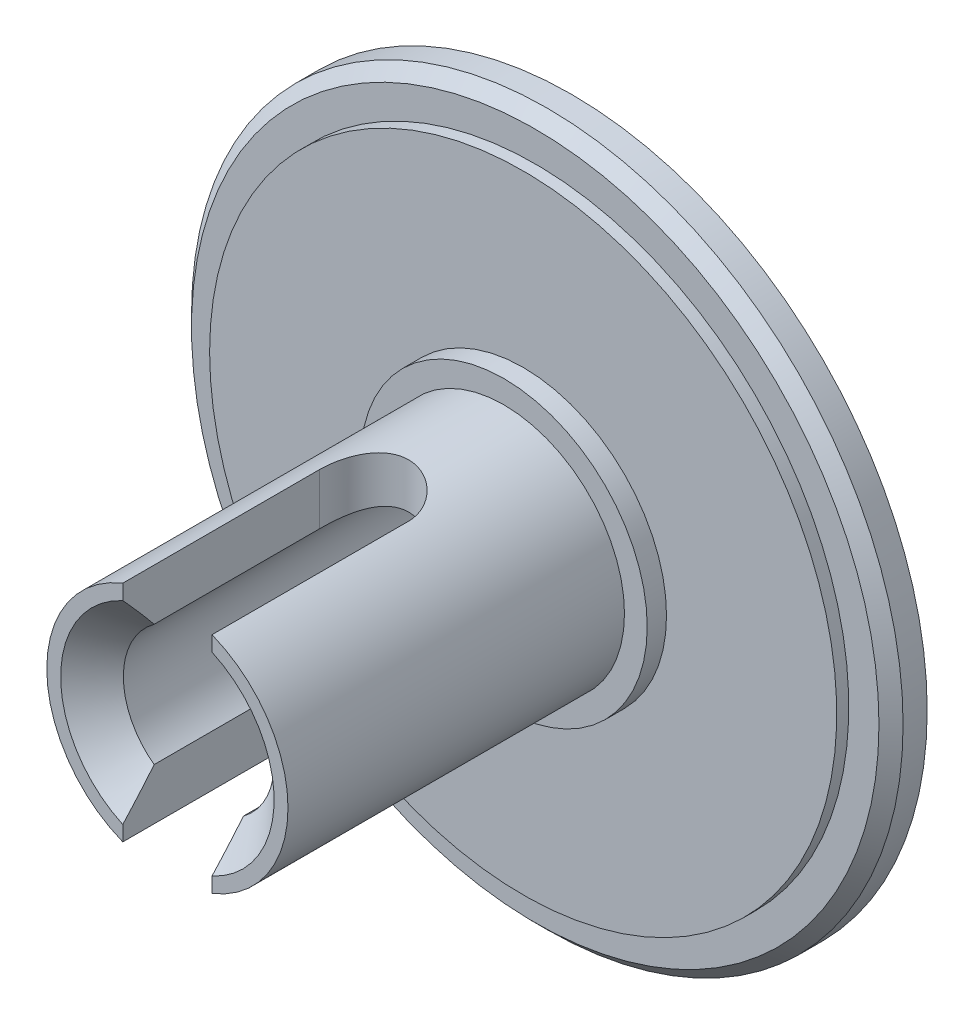
SolidWorks part; units mm, degrees
material "PVC hart"
ref_plane "Ebene vorne" through (0, 0, 0) normal (0, 0, 1) x (1, 0, 0)
ref_plane "Ebene oben" through (0, 0, 0) normal (0, 1, 0) x (1, 0, 0)
ref_plane "Ebene rechts" through (0, 0, 0) normal (1, 0, 0) x (0, 0, -1)
sketch "Skizze2" plane through (0, 0, 0) normal (1, 0, 0) x (0, 0, -1)
  line L0 (10.6064, 0) -> (-45.5592, 0) construction
  line L1 (0, 14.75) -> (-1.5, 14.75)
  line L2 (-1.5, 14.75) -> (-1.5, 13)
  line L3 (-1.5, 13) -> (-2, 13)
  line L4 (-2, 13) -> (-2, 5.9425)
  line L5 (0.5, 7.5) -> (0, 7.5)
  line L6 (0.5, 7.5) -> (0.5, 9.5)
  line L7 (0.5, 9.5) -> (0, 9.5)
  line L8 (0, 9.5) -> (0, 12.65)
  line L9 (0, 7.5) -> (0, 2.5)
  line L10 (0, 2.5) -> (5.25, 2.5)
  line L11 (5.25, 2.5) -> (5.25, 0.9)
  line L12 (5.25, 0.9) -> (-2.65, 0.9)
  line L13 (-2.65, 0.9) -> (-2.65, 3.125)
  line L14 (-2.65, 3.125) -> (-16.75, 3.125)
  line L15 (-16.75, 3.125) -> (-16.75, 5)
  line L16 (-16.75, 5) -> (-2.8, 5)
  line L17 (0, 2.5) -> (0, 0) construction
  line L18 (0, 14.15) -> (-0.8, 14.15)
  line L19 (-0.8, 14.15) -> (-0.8, 12.65)
  line L20 (-0.8, 12.65) -> (0, 12.65)
  line L21 (0, 14.15) -> (0, 14.75)
  line L22 (-2.8, 5) -> (-2.8, 5.9425)
  line L23 (-2.8, 5.9425) -> (-2, 5.9425)
  dimension "D1" = 29.5
  dimension "D2" = 26
  dimension "D3" = 2
  dimension "D4" = 1.5
  dimension "D5" = 2.5
  dimension "D6" = 17.25
  dimension "D7" = 10
  dimension "D8" = 22
  dimension "D9" = 14.1
  dimension "D10" = 19
  dimension "D11" = 15
  dimension "D12" = 1.8
  dimension "D13" = 5
  dimension "D14" = 6.25
  dimension "D15" = 25.3
  dimension "D16" = 1.5
  dimension "D17" = 0.7
  dimension "D18" = 11.8851
  dimension "D19" = 0.8
revolve "Rotation1" add sketch "Skizze2" angle 360 about L0
chamfer "Fase1" distance 0.5 angle 45 1 edges at (-14.75, 0, 1.5)
chamfer "Fase2" distance 1.3 angle 45 1 edges at (-3.125, 0, 16.75)
sketch "Skizze3" plane through (0, 0, 0) normal (0, 1, 0) x (1, 0, 0)
  line L0 (0, -8.6) -> (0, -16.75) construction
  line L1 (1.85, -8.6) -> (1.85, -16.75)
  line L2 (-1.85, -8.6) -> (-1.85, -16.75)
  line L3 (-5, -16.75) -> (5, -16.75) construction
  arc A0 (1.85, -8.6) -> (-1.85, -8.6) centre (0, -8.6) ccw
  arc A1 (-1.85, -16.75) -> (1.85, -16.75) centre (0, -16.75) ccw
  point P2 (0, -12.675)
  point P7 (0, -6.75)
  dimension "D1" = 10
  dimension "D2" = 3.7
extrude "Schnitt-Linear austragen1" cut sketch "Skizze3" against normal through all and the other way through all
sketch "Skizze4" plane through (0, 0, -0.5) normal (0, 0, -1) x (-1, 0, 0)
  line L0 (0, 8.5) -> (0, -8.5) construction
  line L1 (-10, 8.5) -> (10, 8.5)
  line L2 (-10, 8.5) -> (-10, -8.5)
  line L3 (-10, -8.5) -> (10, -8.5)
  line L4 (10, 8.5) -> (10, -8.5)
  dimension "D1" = 20
  dimension "D2" = 17
extrude "Schnitt-Linear austragen2" cut sketch "Skizze4" against normal up to surface (0.5 mm away) flip side to cut up to face at (-12.65, 0, 0)
